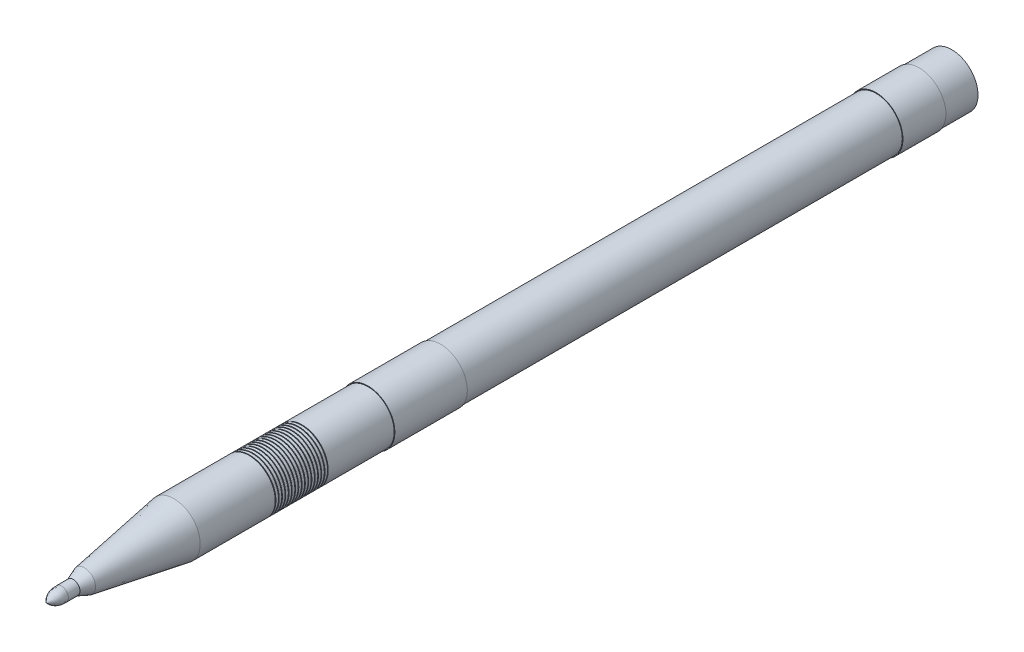
SolidWorks part; units mm, degrees
ref_plane "Front Plane" through (0, 0, 0) normal (0, 0, 1) x (1, 0, 0)
ref_plane "Top Plane" through (0, 0, 0) normal (0, 1, 0) x (1, 0, 0)
ref_plane "Right Plane" through (0, 0, 0) normal (1, 0, 0) x (0, 0, -1)
sketch "Sketch1" plane through (0, 0, 0) normal (1, 0, 0) x (0, 0, -1)
  line L0 (223.9914, -274.4322) -> (1458.509, -274.4322) construction
  line L1 (0, 0) -> (1384, 0)
  line L2 (310, 40) -> (310, 38)
  line L3 (310, 38) -> (311, 38)
  line L4 (311, 38) -> (311, 40)
  line L5 (315, 40) -> (315, 38)
  line L6 (316, 38) -> (316, 40)
  line L7 (315, 38) -> (316, 38)
  line L8 (325, 38) -> (326, 38)
  line L9 (320, 38) -> (321, 38)
  line L10 (325, 40) -> (325, 38)
  line L11 (326, 38) -> (326, 40)
  line L12 (321, 38) -> (321, 40)
  line L13 (320, 40) -> (320, 38)
  line L14 (340, 40) -> (340, 38)
  line L15 (330, 38) -> (331, 38)
  line L16 (0, 0) -> (1384, 0) construction
  line L17 (23.3825, 10.4594) -> (41.1187, 10.4594)
  line L18 (41.1187, 10.4594) -> (58.3224, 17.1346)
  line L19 (58.3224, 17.1346) -> (195.2739, 40)
  line L20 (195.2739, 40) -> (310, 40)
  line L21 (491.8146, 40) -> (491.8146, 41)
  line L22 (491.8146, 41) -> (602.5527, 41)
  line L23 (331, 38) -> (331, 40)
  line L24 (602.5527, 41) -> (602.5527, 40)
  line L25 (602.5527, 40) -> (1268.2938, 40)
  line L26 (1268.2938, 40) -> (1268.2938, 41)
  line L27 (1268.2938, 41) -> (1334, 41)
  line L28 (1334, 41) -> (1334, 40)
  line L29 (1334, 40) -> (1384, 40)
  line L30 (1384, 40) -> (1384, 0)
  line L31 (346, 38) -> (346, 40)
  line L32 (336, 38) -> (336, 40)
  line L33 (340, 38) -> (341, 38)
  line L34 (341, 38) -> (341, 40)
  line L35 (330, 40) -> (330, 38)
  line L36 (335, 40) -> (335, 38)
  line L37 (345, 38) -> (346, 38)
  line L38 (335, 38) -> (336, 38)
  line L39 (345, 40) -> (345, 38)
  line L40 (350, 38) -> (351, 38)
  line L41 (380, 38) -> (381, 38)
  line L42 (370, 38) -> (371, 38)
  line L43 (376, 38) -> (376, 40)
  line L44 (355, 38) -> (356, 38)
  line L45 (361, 38) -> (361, 40)
  line L46 (355, 40) -> (355, 38)
  line L47 (360, 40) -> (360, 38)
  line L48 (371, 38) -> (371, 40)
  line L49 (370, 40) -> (370, 38)
  line L50 (381, 38) -> (381, 40)
  line L51 (350, 40) -> (350, 38)
  line L52 (365, 40) -> (365, 38)
  line L53 (375, 40) -> (375, 38)
  line L54 (366, 38) -> (366, 40)
  line L55 (360, 38) -> (361, 38)
  line L56 (356, 38) -> (356, 40)
  line L57 (365, 38) -> (366, 38)
  line L58 (380, 40) -> (380, 38)
  line L59 (386, 38) -> (386, 40)
  line L60 (385, 38) -> (386, 38)
  line L61 (351, 38) -> (351, 40)
  line L62 (375, 38) -> (376, 38)
  line L63 (385, 38) -> (385, 40)
  line L64 (391, 38) -> (391, 40)
  line L65 (390, 38) -> (391, 38)
  line L66 (390, 38) -> (390, 40)
  line L67 (311, 40) -> (315, 40)
  line L68 (316, 40) -> (320, 40)
  line L69 (321, 40) -> (325, 40)
  line L70 (326, 40) -> (330, 40)
  line L71 (331, 40) -> (335, 40)
  line L72 (336, 40) -> (340, 40)
  line L73 (341, 40) -> (345, 40)
  line L74 (346, 40) -> (350, 40)
  line L75 (351, 40) -> (355, 40)
  line L76 (356, 40) -> (360, 40)
  line L77 (361, 40) -> (365, 40)
  line L78 (366, 40) -> (370, 40)
  line L79 (371, 40) -> (375, 40)
  line L80 (376, 40) -> (380, 40)
  line L81 (381, 40) -> (385, 40)
  line L82 (386, 40) -> (390, 40)
  line L83 (391, 40) -> (491.8146, 40)
  spline S1 degree 2 poles (0, 0) (8.503, 11.3119) (23.3825, 10.4594) knots 0 0 0 1 1 1
  point P21 (547.1837, 41)
  point P39 (1301.1469, 41)
  dimension "D1" = 1384
  dimension "D2" = 40
  dimension "D3" = 41
  dimension "D4" = 40
  dimension "D5" = 40
  dimension "D6" = 41
  dimension "D7" = 50
  dimension "D8" = 310
  dimension "D9" = 4
  dimension "D10" = 4
  dimension "D11" = 4
  dimension "D12" = 4
  dimension "D13" = 4
  dimension "D14" = 4
  dimension "D15" = 4
  dimension "D16" = 4
  dimension "D17" = 4
  dimension "D18" = 4
  dimension "D19" = 4
  dimension "D20" = 4
  dimension "D21" = 4
  dimension "D22" = 4
  dimension "D23" = 4
  dimension "D24" = 4
revolve "Revolve1" add sketch "Sketch1" angle 360 about L1
ref_plane "Plane1" through (0, 40, 0) normal (0, 1, 0) x (1, 0, 0)
sketch "Sketch2" plane through (0, 40, 0) normal (0, 1, 0) x (1, 0, 0)
  line L0 (40, 1384) -> (-40, 1384) construction
  line L1 (0, 1384) -> (0, 1359) construction
  circle A0 centre (0, 1359) radius 0.25
  dimension "D1" = 25
extrude "Cut-Extrude1" cut sketch "Sketch2" against normal blind 2
